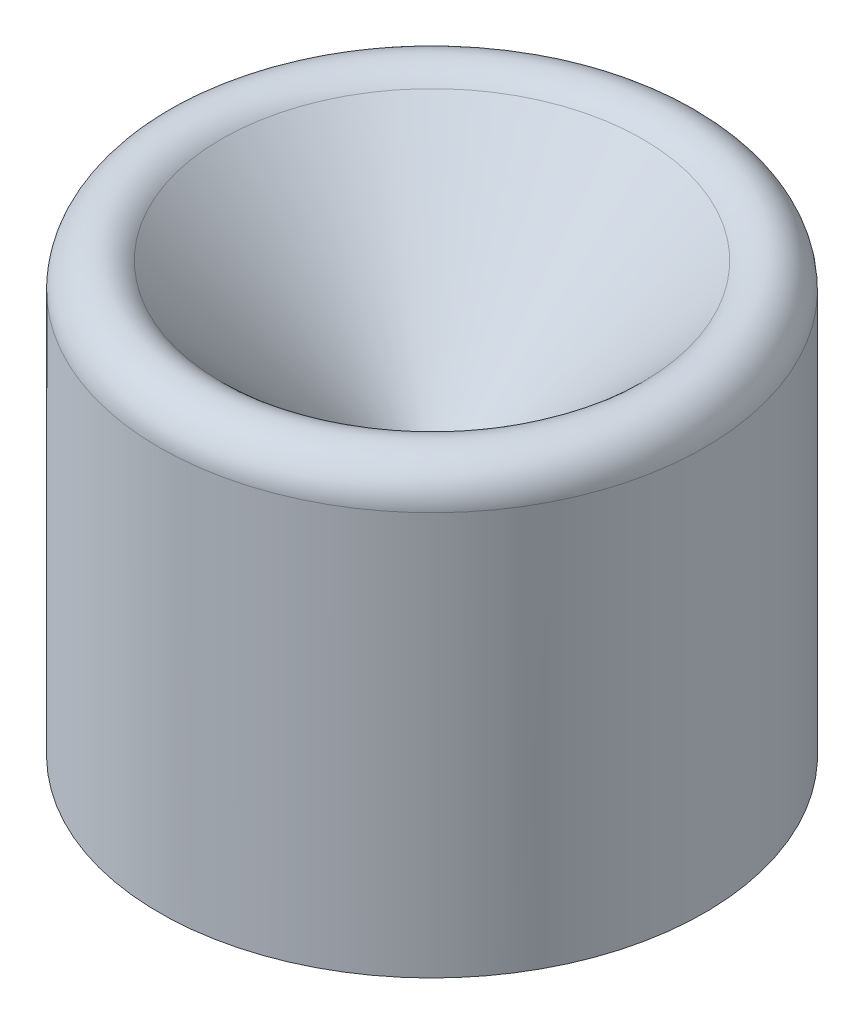
SolidWorks part; units mm, degrees
ref_plane "Front Plane" through (0, 0, 0) normal (0, 0, 1) x (1, 0, 0)
ref_plane "Top Plane" through (0, 0, 0) normal (0, 1, 0) x (1, 0, 0)
ref_plane "Right Plane" through (0, 0, 0) normal (1, 0, 0) x (0, 0, -1)
sketch "Sketch1" plane through (0, 0, 0) normal (1, 0, 0) x (0, 0, -1)
  line L0 (0, 0) -> (15, 15)
  line L1 (15, 15) -> (15, -12)
  line L2 (15, -12) -> (3, -12)
  line L3 (3, -12) -> (3, -6)
  line L4 (3, -6) -> (0, -6)
  line L5 (0, -6) -> (0, 0)
  point P3 (0, 0)
  dimension "D1" = 135
  dimension "D2" = 3
  dimension "D3" = 6
  dimension "D4" = 12
  dimension "D5" = 15
revolve "Revolve1" add sketch "Sketch1" angle 360 about L5
fillet "Fillet1" radius 2 1 edges at (0, 15, -15)
chamfer "Chamfer1" distance 1 angle 45 1 edges at (0, -12, -3)
